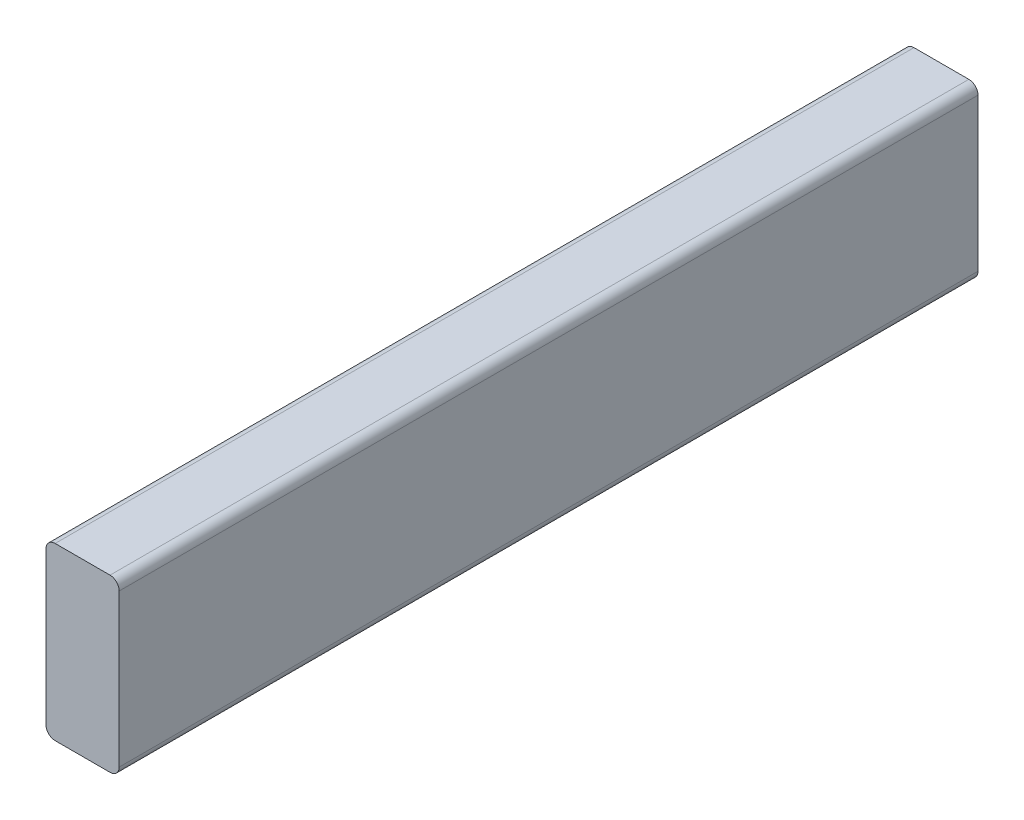
SolidWorks part; units mm, degrees
material "Pine"
ref_plane "Front Plane" through (0, 0, 0) normal (0, 0, 1) x (1, 0, 0)
ref_plane "Top Plane" through (0, 0, 0) normal (0, 1, 0) x (1, 0, 0)
ref_plane "Right Plane" through (0, 0, 0) normal (1, 0, 0) x (0, 0, -1)
sketch "Sketch1" plane through (0, 0, 0) normal (0, 0, 1) x (1, 0, 0)
  line L1 (-204.9322, 440.5504) -> (-166.8322, 440.5504)
  line L2 (-204.9322, 440.5504) -> (-204.9322, 351.6504)
  line L3 (-204.9322, 351.6504) -> (-166.8322, 351.6504)
  line L4 (-166.8322, 440.5504) -> (-166.8322, 351.6504)
extrude "Boss-Extrude1" add sketch "Sketch1" against normal up to surface (446.9765 mm away)
fillet "Fillet1" radius 4.7625 4 edges at (-204.9322, 351.6504, -223.4883) (-166.8322, 351.6504, -223.4883) (-204.9322, 440.5504, -223.4883) (-166.8322, 440.5504, -223.4883)
